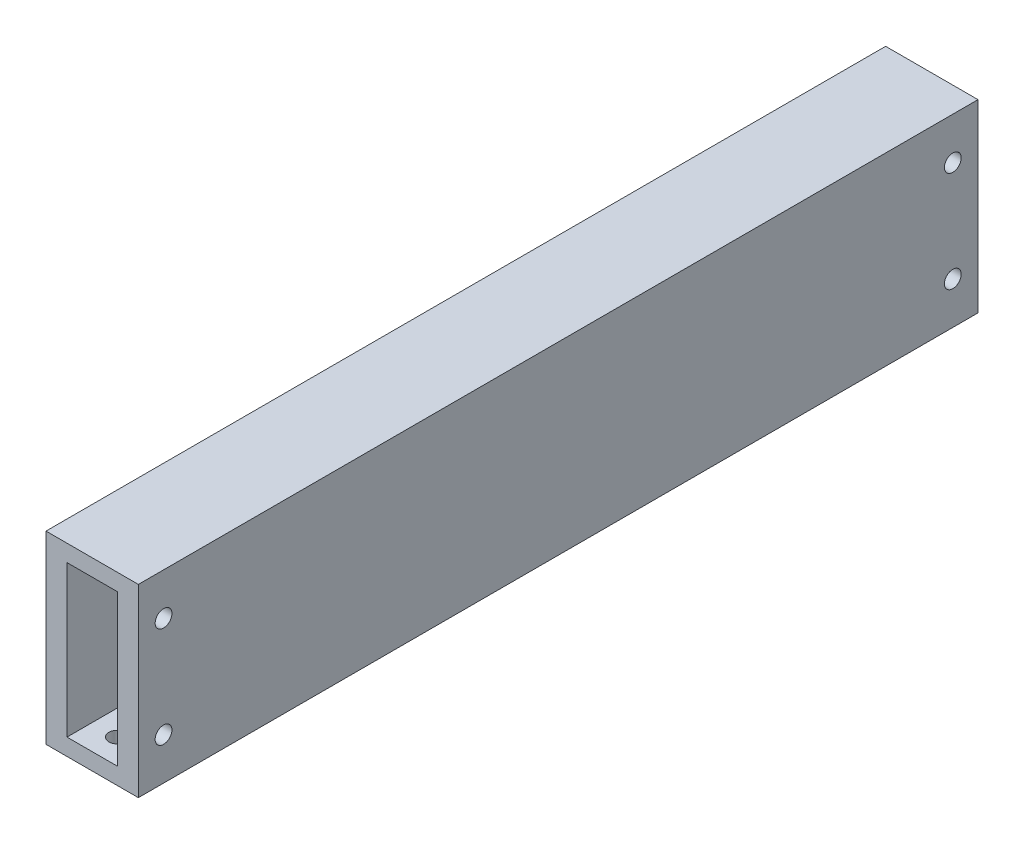
SolidWorks part; units mm, degrees
material "1060 Alloy"
ref_plane "Front Plane" through (0, 0, 0) normal (0, 0, 1) x (1, 0, 0)
ref_plane "Top Plane" through (0, 0, 0) normal (0, 1, 0) x (1, 0, 0)
ref_plane "Right Plane" through (0, 0, 0) normal (1, 0, 0) x (0, 0, -1)
sketch "Sketch1" plane through (0, 0, 0) normal (0, 1, 0) x (1, 0, 0)
  line L1 (-3.4013, -34.4655) -> (51.5987, -34.4655)
  line L2 (-3.4013, -34.4655) -> (-3.4013, 465.5345)
  line L3 (-3.4013, 465.5345) -> (51.5987, 465.5345)
  line L4 (51.5987, -34.4655) -> (51.5987, 465.5345)
  dimension "D1" = 500
  dimension "D2" = 55
extrude "Boss-Extrude1" add sketch "Sketch1" along normal blind 110
ref_plane "Plane1" through (0, 0, 34.4655) normal (0, 0, 1) x (1, 0, 0)
sketch "Sketch2" plane through (0, 0, 34.4655) normal (0, 0, 1) x (1, 0, 0)
  line L0 (-3.4013, 55) -> (51.5987, 55)
  line L1 (-3.4013, 110) -> (-3.4013, 0) construction
  line L2 (51.5987, 110) -> (51.5987, 0) construction
  line L3 (24.0987, 110) -> (24.0987, 0)
  line L4 (-3.4013, 110) -> (51.5987, 110) construction
  line L5 (-3.4013, 0) -> (51.5987, 0) construction
  line L7 (9.0987, 10) -> (39.0987, 10)
  line L8 (9.0987, 10) -> (9.0987, 100)
  line L9 (9.0987, 100) -> (39.0987, 100)
  line L10 (39.0987, 10) -> (39.0987, 100)
  line L11 (9.0987, 10) -> (39.0987, 100) construction
  line L12 (9.0987, 100) -> (39.0987, 10) construction
  point P12 (24.0987, 55)
extrude "Cut-Extrude1" cut sketch "Sketch2" against normal blind 500 contours L9 L8 L0 L3 | L0 L10 L9 L3 | L7 L10 L0 L3 | L8 L7 L3 L0
ref_plane "Plane2" through (0, 10, 0) normal (0, 1, 0) x (1, 0, 0)
sketch "Sketch3" plane through (0, 10, 0) normal (0, 1, 0) x (1, 0, 0)
  line L0 (39.0987, 465.5345) -> (39.0987, -34.4655) construction
  line L1 (9.0987, -34.4655) -> (39.0987, -34.4655) construction
  line L2 (9.0987, 465.5345) -> (39.0987, 465.5345) construction
  line L3 (9.0987, 465.5345) -> (9.0987, -34.4655) construction
  point P0 (24.0987, -19.4655)
  point P5 (24.0987, 450.5345)
  dimension "D1" = 15
  dimension "D2" = 15
  dimension "D3" = 15
  dimension "D4" = 15
hole_wizard "M10x1.0 Tapped Hole1" positions "Sketch11" profile "Sketch10" tap size "M10x1.0" standard "ANSI Metric"
sketch "Sketch11" plane through (0, 10, 0) normal (0, 1, 0) x (1, 0, 0)
  point P0 (24.0987, 450.5345)
  point P3 (24.0987, -19.4655)
sketch "Sketch10" plane through (24.0987, 10, -450.5345) normal (1, 0, 0) x (0, 0, 1)
  line L0 (0, 0) -> (0, 25.7039)
  line L1 (0, 25.7039) -> (4.5, 23)
  line L2 (4.5, 23) -> (4.5, 20)
  line L3 (4.5, 20) -> (5, 20)
  line L4 (5, 20) -> (5, 0)
  line L5 (5, 0) -> (0, 0)
  line L10 (0, 25.7039) -> (-4.5, 23) construction
  line L11 (0, -6.35) -> (0, 107.95) construction
  dimension "Tap Drill Dia." = 9
  dimension "Tap Drill Depth" = 23
  dimension "Thread Major Dia." = 10
  dimension "Thread Depth" = 20
  dimension "Drill Angle" = 118
ref_plane "Plane4" through (51.5987, 0, 0) normal (1, 0, 0) x (0, 0, -1)
sketch "Sketch12" plane through (51.5987, 0, 0) normal (1, 0, 0) x (0, 0, -1)
  line L0 (-34.4655, 110) -> (465.5345, 110) construction
  line L1 (465.5345, 110) -> (465.5345, 0) construction
  line L2 (-34.4655, 0) -> (465.5345, 0) construction
  line L3 (-34.4655, 110) -> (-34.4655, 0) construction
  point P0 (450.5345, 85)
  point P1 (450.5345, 25)
  point P8 (-19.4655, 85)
  point P9 (-19.4655, 25)
  dimension "D1" = 25
  dimension "D2" = 15
  dimension "D3" = 15
  dimension "D4" = 25
  dimension "D5" = 25
  dimension "D6" = 25
  dimension "D7" = 15
  dimension "D8" = 15
hole_wizard "M10x1.0 Tapped Hole2" positions "3DSketch2" profile "Sketch19" tap size "M10x1.0" standard "ANSI Metric"
sketch3d "3DSketch2"
  point P0 (233.9478, 74.11, 0)
  point P2 (51.5987, 85, -450.5345)
  point P5 (51.5987, 25, -450.5345)
  point P8 (51.5987, 85, 19.4655)
  point P11 (51.5987, 25, 19.4655)
sketch "Sketch19" plane through (51.5987, 85, -450.5345) normal (0, 1, 0) x (0, 0, -1)
  line L0 (0, 0) -> (0, 25.7039)
  line L1 (0, 25.7039) -> (4.5, 23)
  line L2 (4.5, 23) -> (4.5, 20)
  line L3 (4.5, 20) -> (5, 20)
  line L4 (5, 20) -> (5, 0)
  line L5 (5, 0) -> (0, 0)
  line L10 (0, 25.7039) -> (-4.5, 23) construction
  line L11 (0, -6.35) -> (0, 107.95) construction
  dimension "Tap Drill Dia." = 9
  dimension "Tap Drill Depth" = 23
  dimension "Thread Major Dia." = 10
  dimension "Thread Depth" = 20
  dimension "Drill Angle" = 118
